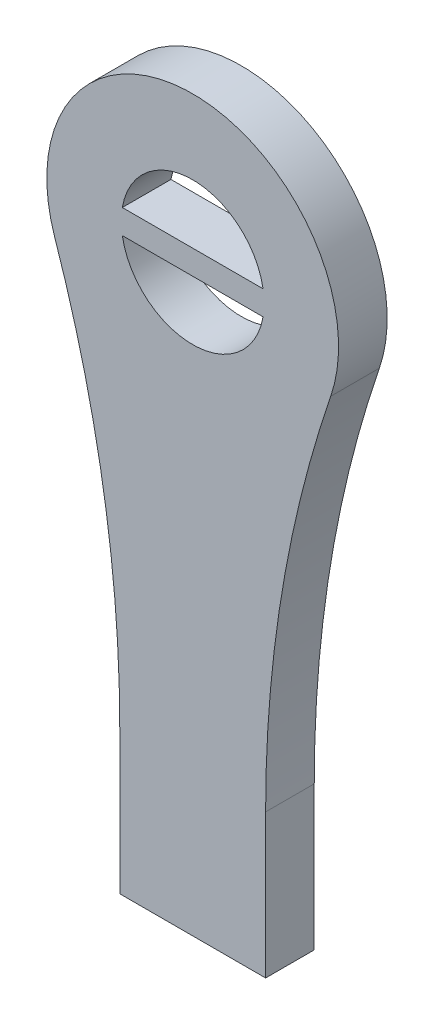
SolidWorks part; units mm, degrees
ref_plane "Front Plane" through (0, 0, 0) normal (0, 0, 1) x (1, 0, 0)
ref_plane "Top Plane" through (0, 0, 0) normal (0, 1, 0) x (1, 0, 0)
ref_plane "Right Plane" through (0, 0, 0) normal (1, 0, 0) x (0, 0, -1)
sketch "Model" plane through (0, 0, 0) normal (0, 0, 1) x (1, 0, 0)
  line L0 (58.0831, -82) -> (58.0831, -87.9169)
  line L1 (58.0831, -87.9169) -> (52.0831, -87.9169)
  line L2 (52.0831, -87.9169) -> (52.0831, -82)
  line L3 (52.1885, -64.4169) -> (57.9778, -64.4169)
  line L4 (57.9778, -63.4169) -> (52.1885, -63.4169)
  arc A0 (52.0831, -82) -> (49.4046, -65.8543) centre (2.0831, -82) ccw
  arc A1 (60.7617, -65.8543) -> (49.4046, -65.8543) centre (55.0831, -63.9169) ccw
  arc A2 (60.7617, -65.8543) -> (58.0831, -82) centre (108.0831, -82) ccw
  arc A3 (52.1885, -64.4169) -> (57.9778, -64.4169) centre (55.0831, -63.9169) ccw
  arc A4 (57.9778, -63.4169) -> (52.1885, -63.4169) centre (55.0831, -63.9169) ccw
extrude "Boss-Extrude1" add sketch "Model" along normal blind 2
